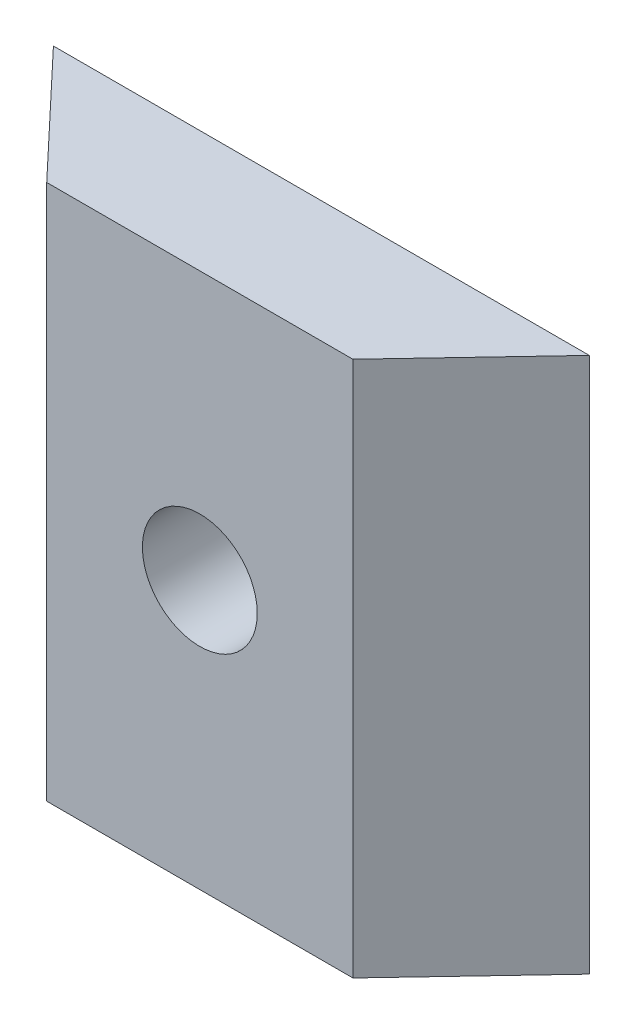
SolidWorks part; units mm, degrees
ref_plane "Plano frontal" through (0, 0, 0) normal (0, 0, 1) x (1, 0, 0)
ref_plane "Plano superior" through (0, 0, 0) normal (0, 1, 0) x (1, 0, 0)
ref_plane "Plano direito" through (0, 0, 0) normal (1, 0, 0) x (0, 0, -1)
sketch "Esboço1" plane through (0, 0, 0) normal (0, 0, 1) x (1, 0, 0)
  line L1 (-7, 7) -> (7, 7)
  line L2 (-7, 7) -> (-7, -7)
  line L3 (-7, -7) -> (7, -7)
  line L4 (7, 7) -> (7, -7)
  line L5 (-7, 7) -> (7, -7) construction
  line L6 (-7, -7) -> (7, 7) construction
  point P0 (0, 0)
  dimension "D1" = 14
  dimension "D2" = 14
extrude "Ressalto-extrusão1" add sketch "Esboço1" along normal blind 3.175
sketch "Esboço2" plane through (0, -7, 0) normal (0, -1, 0) x (1, 0, 0)
  line L0 (-4, 3.175) -> (-7, 3.175)
  line L1 (-7, 3.175) -> (7, 3.175) construction
  line L2 (-7, 3.175) -> (-7, 0)
  line L3 (-7, 0) -> (-4, 3.175)
  line L4 (4, 3.175) -> (7, 3.175)
  line L5 (7, 3.175) -> (7, 0)
  line L6 (7, 0) -> (4, 3.175)
  dimension "D1" = 3
  dimension "D2" = 3
extrude "Corte-extrusão1" cut sketch "Esboço2" against normal through all
sketch "Esboço10" plane through (0, 0, 3.175) normal (0, 0, 1) x (1, 0, 0)
  circle A0 centre (0, 0) radius 1.5
  dimension "FURO" = 3
extrude "Corte-extrusão2" cut sketch "Esboço10" against normal through all
cosmetic thread "Representação de rosca1" [suppressed] parameters "D2"=5
cosmetic thread "Representação de rosca2" [suppressed] parameters "D2"=5
cosmetic thread "Representação de rosca3" [suppressed] parameters "D2"=8
cosmetic thread "Representação de rosca4" parameters "D2"=4
